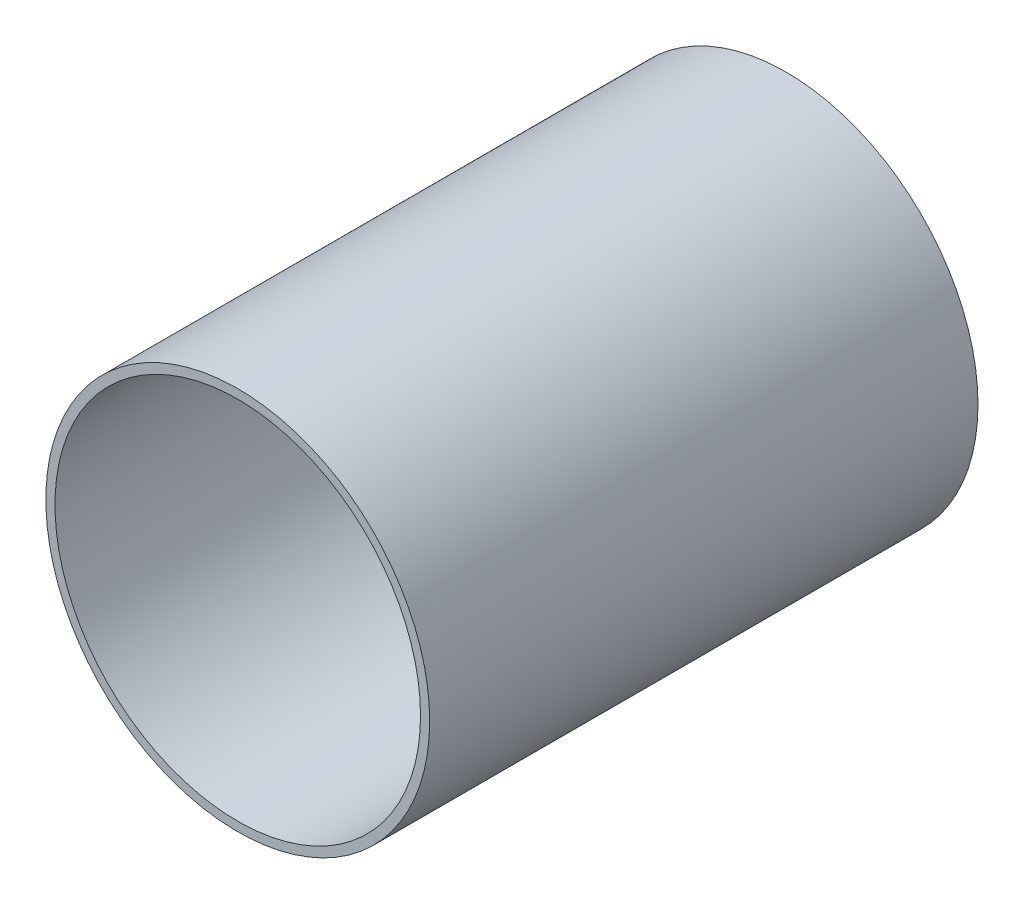
SolidWorks part; units mm, degrees
ref_plane "Front Plane" through (0, 0, 0) normal (0, 0, 1) x (1, 0, 0)
ref_plane "Top Plane" through (0, 0, 0) normal (0, 1, 0) x (1, 0, 0)
ref_plane "Right Plane" through (0, 0, 0) normal (1, 0, 0) x (0, 0, -1)
sketch "Sketch1" plane through (0, 0, 0) normal (0, 0, 1) x (1, 0, 0)
  circle A0 centre (0, 0) radius 50.8
  circle A1 centre (0, 0) radius 53.34
  dimension "D1" = 101.6
  dimension "D2" = 2.54
extrude "Boss-Extrude1" add sketch "Sketch1" along normal blind 152.4
